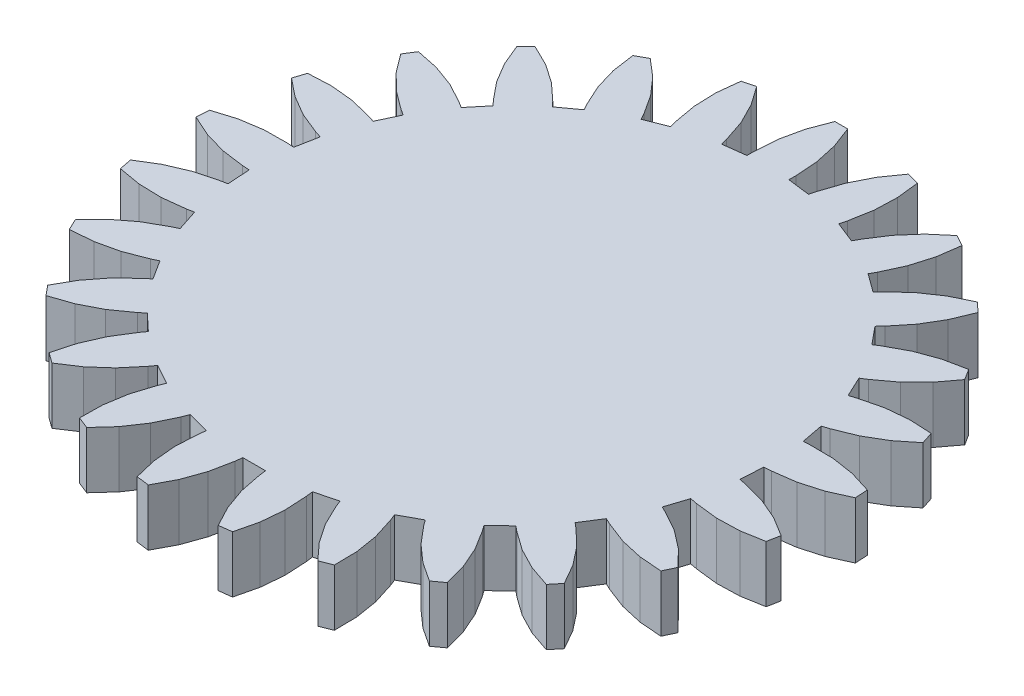
SolidWorks part; units mm, degrees
ref_plane "Alzado" through (0, 0, 0) normal (0, 0, 1) x (1, 0, 0)
ref_plane "Planta" through (0, 0, 0) normal (0, 1, 0) x (1, 0, 0)
ref_plane "Vista lateral" through (0, 0, 0) normal (1, 0, 0) x (0, 0, -1)
ref_plane "Plano1" through (0, 0, 0) normal (0, -1, 0) x (1, 0, 0)
sketch "Croquis1" plane through (0, 0, 0) normal (0, -1, 0) x (1, 0, 0)
  line L0 (59.9729, 13.0996) -> (60.4384, 12.2529)
  line L1 (60.4384, 12.2529) -> (62.1486, 9.6129)
  line L2 (62.1486, 9.6129) -> (64.2209, 7.2465)
  line L3 (64.2209, 7.2465) -> (66.6121, 5.2029)
  line L4 (66.6121, 5.2029) -> (68.1588, 6.0532)
  line L5 (68.1588, 6.0532) -> (67.7145, 9.1672)
  line L6 (67.7145, 9.1672) -> (66.8269, 12.1848)
  line L7 (66.8269, 12.1848) -> (65.5143, 15.0434)
  line L8 (65.5143, 15.0434) -> (65.0488, 15.8901)
  line L9 (65.0488, 15.8901) -> (67.5748, 17.7253)
  line L10 (67.5748, 17.7253) -> (68.2362, 17.021)
  line L11 (68.2362, 17.021) -> (70.5492, 14.8893)
  line L12 (70.5492, 14.8893) -> (73.1449, 13.1126)
  line L13 (73.1449, 13.1126) -> (75.9692, 11.7278)
  line L14 (75.9692, 11.7278) -> (77.2558, 12.936)
  line L15 (77.2558, 12.936) -> (76.0511, 15.8417)
  line L16 (76.0511, 15.8417) -> (74.4409, 18.5438)
  line L17 (74.4409, 18.5438) -> (72.4587, 20.9861)
  line L18 (72.4587, 20.9861) -> (71.7973, 21.6905)
  line L19 (71.7973, 21.6905) -> (73.7875, 24.0962)
  line L20 (73.7875, 24.0962) -> (74.6033, 23.5785)
  line L21 (74.6033, 23.5785) -> (77.3738, 22.089)
  line L22 (77.3738, 22.089) -> (80.3297, 21.0136)
  line L23 (80.3297, 21.0136) -> (83.4097, 20.3748)
  line L24 (83.4097, 20.3748) -> (84.3554, 21.865)
  line L25 (84.3554, 21.865) -> (82.466, 24.3798)
  line L26 (82.466, 24.3798) -> (80.2343, 26.5966)
  line L27 (80.2343, 26.5966) -> (77.707, 28.4692)
  line L28 (77.707, 28.4692) -> (76.8912, 28.9869)
  line L29 (76.8912, 28.9869) -> (78.2206, 31.812)
  line L30 (78.2206, 31.812) -> (79.1395, 31.5135)
  line L31 (79.1395, 31.5135) -> (82.1934, 30.7597)
  line L32 (82.1934, 30.7597) -> (85.3239, 30.4533)
  line L33 (85.3239, 30.4533) -> (88.466, 30.6004)
  line L34 (88.466, 30.6004) -> (89.0114, 32.279)
  line L35 (89.0114, 32.279) -> (86.5559, 34.2449)
  line L36 (86.5559, 34.2449) -> (83.8431, 35.8371)
  line L37 (83.8431, 35.8371) -> (80.9295, 37.0223)
  line L38 (80.9295, 37.0223) -> (80.0106, 37.3209)
  line L39 (80.0106, 37.3209) -> (80.5956, 40.3879)
  line L40 (80.5956, 40.3879) -> (81.5599, 40.3272)
  line L41 (81.5599, 40.3272) -> (84.7053, 40.3567)
  line L42 (84.7053, 40.3567) -> (87.8137, 40.8384)
  line L43 (87.8137, 40.8384) -> (90.8204, 41.7623)
  line L44 (90.8204, 41.7623) -> (90.9313, 43.5238)
  line L45 (90.9313, 43.5238) -> (88.064, 44.8173)
  line L46 (88.064, 44.8173) -> (85.0405, 45.6848)
  line L47 (85.0405, 45.6848) -> (81.9236, 46.1082)
  line L48 (81.9236, 46.1082) -> (80.9593, 46.1688)
  line L49 (80.9593, 46.1688) -> (80.7633, 49.285)
  line L50 (80.7633, 49.285) -> (81.7124, 49.466)
  line L51 (81.7124, 49.466) -> (84.7516, 50.2768)
  line L52 (84.7516, 50.2768) -> (87.6425, 51.5163)
  line L53 (87.6425, 51.5163) -> (90.3251, 53.159)
  line L54 (90.3251, 53.159) -> (89.9943, 54.8927)
  line L55 (89.9943, 54.8927) -> (86.8955, 55.4325)
  line L56 (86.8955, 55.4325) -> (83.7512, 55.5208)
  line L57 (83.7512, 55.5208) -> (80.627, 55.1558)
  line L58 (80.627, 55.1558) -> (79.6779, 54.9747)
  line L59 (79.6779, 54.9747) -> (78.7131, 57.9442)
  line L60 (78.7131, 57.9442) -> (79.5873, 58.3556)
  line L61 (79.5873, 58.3556) -> (82.3294, 59.8967)
  line L62 (82.3294, 59.8967) -> (84.8213, 61.8163)
  line L63 (84.8213, 61.8163) -> (87.011, 64.0744)
  line L64 (87.011, 64.0744) -> (86.2595, 65.6715)
  line L65 (86.2595, 65.6715) -> (83.1238, 65.4236)
  line L66 (83.1238, 65.4236) -> (80.0563, 64.7272)
  line L67 (80.0563, 64.7272) -> (77.121, 63.5967)
  line L68 (77.121, 63.5967) -> (76.2468, 63.1853)
  line L69 (76.2468, 63.1853) -> (74.5738, 65.8216)
  line L70 (74.5738, 65.8216) -> (75.3182, 66.4374)
  line L71 (75.3182, 66.4374) -> (77.5909, 68.6121)
  line L72 (77.5909, 68.6121) -> (79.5271, 71.091)
  line L73 (79.5271, 71.091) -> (81.0865, 73.8228)
  line L74 (81.0865, 73.8228) -> (79.9615, 75.1828)
  line L75 (79.9615, 75.1828) -> (76.9859, 74.1629)
  line L76 (76.9859, 74.1629) -> (74.188, 72.7255)
  line L77 (74.188, 72.7255) -> (71.626, 70.9005)
  line L78 (71.626, 70.9005) -> (70.8816, 70.2847)
  line L79 (70.8816, 70.2847) -> (68.6055, 72.422)
  line L80 (68.6055, 72.422) -> (69.1734, 73.2037)
  line L81 (69.1734, 73.2037) -> (70.8339, 75.8752)
  line L82 (70.8339, 75.8752) -> (72.0928, 78.7578)
  line L83 (72.0928, 78.7578) -> (72.9238, 81.7915)
  line L84 (72.9238, 81.7915) -> (71.4959, 82.829)
  line L85 (71.4959, 82.829) -> (68.8674, 81.1012)
  line L86 (68.8674, 81.1012) -> (66.5149, 79.0131)
  line L87 (66.5149, 79.0131) -> (64.4873, 76.6084)
  line L88 (64.4873, 76.6084) -> (63.9194, 75.8267)
  line L89 (63.9194, 75.8267) -> (61.1833, 77.3309)
  line L90 (61.1833, 77.3309) -> (61.539, 78.2292)
  line L91 (61.539, 78.2292) -> (62.4829, 81.2297)
  line L92 (62.4829, 81.2297) -> (62.9854, 84.3349)
  line L93 (62.9854, 84.3349) -> (63.0358, 87.48)
  line L94 (63.0358, 87.48) -> (61.3948, 88.1297)
  line L95 (61.3948, 88.1297) -> (59.2786, 85.8025)
  line L96 (59.2786, 85.8025) -> (57.5192, 83.195)
  line L97 (57.5192, 83.195) -> (56.1534, 80.3615)
  line L98 (56.1534, 80.3615) -> (55.7977, 79.4632)
  line L99 (55.7977, 79.4632) -> (52.7735, 80.2397)
  line L100 (52.7735, 80.2397) -> (52.8946, 81.1982)
  line L101 (52.8946, 81.1982) -> (53.0627, 84.3393)
  line L102 (53.0627, 84.3393) -> (52.7771, 87.4718)
  line L103 (52.7771, 87.4718) -> (52.0438, 90.5306)
  line L104 (52.0438, 90.5306) -> (50.2927, 90.7518)
  line L105 (50.2927, 90.7518) -> (48.8218, 87.9714)
  line L106 (48.8218, 87.9714) -> (47.7662, 85.0084)
  line L107 (47.7662, 85.0084) -> (47.1479, 81.9242)
  line L108 (47.1479, 81.9242) -> (47.0268, 80.9657)
  line L109 (47.0268, 80.9657) -> (43.9045, 80.9657)
  line L110 (43.9045, 80.9657) -> (43.7834, 81.9242)
  line L111 (43.7834, 81.9242) -> (43.1651, 85.0084)
  line L112 (43.1651, 85.0084) -> (42.1095, 87.9714)
  line L113 (42.1095, 87.9714) -> (40.6385, 90.7518)
  line L114 (40.6385, 90.7518) -> (38.8874, 90.5306)
  line L115 (38.8874, 90.5306) -> (38.1541, 87.4718)
  line L116 (38.1541, 87.4718) -> (37.8686, 84.3393)
  line L117 (37.8686, 84.3393) -> (38.0367, 81.1982)
  line L118 (38.0367, 81.1982) -> (38.1578, 80.2397)
  line L119 (38.1578, 80.2397) -> (35.1336, 79.4632)
  line L120 (35.1336, 79.4632) -> (34.7779, 80.3615)
  line L121 (34.7779, 80.3615) -> (33.412, 83.195)
  line L122 (33.412, 83.195) -> (31.6527, 85.8025)
  line L123 (31.6527, 85.8025) -> (29.5365, 88.1297)
  line L124 (29.5365, 88.1297) -> (27.8954, 87.48)
  line L125 (27.8954, 87.48) -> (27.9459, 84.3349)
  line L126 (27.9459, 84.3349) -> (28.4483, 81.2297)
  line L127 (28.4483, 81.2297) -> (29.3923, 78.2292)
  line L128 (29.3923, 78.2292) -> (29.748, 77.3309)
  line L129 (29.748, 77.3309) -> (27.0119, 75.8267)
  line L130 (27.0119, 75.8267) -> (26.444, 76.6084)
  line L131 (26.444, 76.6084) -> (24.4164, 79.0131)
  line L132 (24.4164, 79.0131) -> (22.0638, 81.1012)
  line L133 (22.0638, 81.1012) -> (19.4354, 82.829)
  line L134 (19.4354, 82.829) -> (18.0074, 81.7915)
  line L135 (18.0074, 81.7915) -> (18.8385, 78.7578)
  line L136 (18.8385, 78.7578) -> (20.0973, 75.8752)
  line L137 (20.0973, 75.8752) -> (21.7578, 73.2037)
  line L138 (21.7578, 73.2037) -> (22.3257, 72.422)
  line L139 (22.3257, 72.422) -> (20.0497, 70.2847)
  line L140 (20.0497, 70.2847) -> (19.3052, 70.9005)
  line L141 (19.3052, 70.9005) -> (16.7433, 72.7255)
  line L142 (16.7433, 72.7255) -> (13.9454, 74.1629)
  line L143 (13.9454, 74.1629) -> (10.9698, 75.1828)
  line L144 (10.9698, 75.1828) -> (9.8447, 73.8228)
  line L145 (9.8447, 73.8228) -> (11.4041, 71.091)
  line L146 (11.4041, 71.091) -> (13.3403, 68.6121)
  line L147 (13.3403, 68.6121) -> (15.613, 66.4374)
  line L148 (15.613, 66.4374) -> (16.3575, 65.8216)
  line L149 (16.3575, 65.8216) -> (14.6845, 63.1853)
  line L150 (14.6845, 63.1853) -> (13.8103, 63.5967)
  line L151 (13.8103, 63.5967) -> (10.8749, 64.7272)
  line L152 (10.8749, 64.7272) -> (7.8075, 65.4236)
  line L153 (7.8075, 65.4236) -> (4.6718, 65.6715)
  line L154 (4.6718, 65.6715) -> (3.9202, 64.0744)
  line L155 (3.9202, 64.0744) -> (6.11, 61.8163)
  line L156 (6.11, 61.8163) -> (8.6019, 59.8967)
  line L157 (8.6019, 59.8967) -> (11.344, 58.3556)
  line L158 (11.344, 58.3556) -> (12.2182, 57.9442)
  line L159 (12.2182, 57.9442) -> (11.2534, 54.9747)
  line L160 (11.2534, 54.9747) -> (10.3043, 55.1558)
  line L161 (10.3043, 55.1558) -> (7.18, 55.5208)
  line L162 (7.18, 55.5208) -> (4.0358, 55.4325)
  line L163 (4.0358, 55.4325) -> (0.9369, 54.8927)
  line L164 (0.9369, 54.8927) -> (0.6062, 53.159)
  line L165 (0.6062, 53.159) -> (3.2887, 51.5163)
  line L166 (3.2887, 51.5163) -> (6.1797, 50.2768)
  line L167 (6.1797, 50.2768) -> (9.2189, 49.466)
  line L168 (9.2189, 49.466) -> (10.168, 49.285)
  line L169 (10.168, 49.285) -> (9.9719, 46.1688)
  line L170 (9.9719, 46.1688) -> (9.0077, 46.1082)
  line L171 (9.0077, 46.1082) -> (5.8908, 45.6848)
  line L172 (5.8908, 45.6848) -> (2.8673, 44.8173)
  line L173 (2.8673, 44.8173) -> (0, 43.5238)
  line L174 (0, 43.5238) -> (0.1108, 41.7623)
  line L175 (0.1108, 41.7623) -> (3.1176, 40.8384)
  line L176 (3.1176, 40.8384) -> (6.226, 40.3567)
  line L177 (6.226, 40.3567) -> (9.3714, 40.3272)
  line L178 (9.3714, 40.3272) -> (10.3356, 40.3879)
  line L179 (10.3356, 40.3879) -> (10.9207, 37.3209)
  line L180 (10.9207, 37.3209) -> (10.0018, 37.0223)
  line L181 (10.0018, 37.0223) -> (7.0881, 35.8371)
  line L182 (7.0881, 35.8371) -> (4.3753, 34.2449)
  line L183 (4.3753, 34.2449) -> (1.9199, 32.279)
  line L184 (1.9199, 32.279) -> (2.4653, 30.6004)
  line L185 (2.4653, 30.6004) -> (5.6073, 30.4533)
  line L186 (5.6073, 30.4533) -> (8.7379, 30.7597)
  line L187 (8.7379, 30.7597) -> (11.7917, 31.5135)
  line L188 (11.7917, 31.5135) -> (12.7106, 31.812)
  line L189 (12.7106, 31.812) -> (14.04, 28.9869)
  line L190 (14.04, 28.9869) -> (13.2243, 28.4692)
  line L191 (13.2243, 28.4692) -> (10.6969, 26.5966)
  line L192 (10.6969, 26.5966) -> (8.4653, 24.3798)
  line L193 (8.4653, 24.3798) -> (6.5758, 21.865)
  line L194 (6.5758, 21.865) -> (7.5216, 20.3748)
  line L195 (7.5216, 20.3748) -> (10.6015, 21.0136)
  line L196 (10.6015, 21.0136) -> (13.5575, 22.089)
  line L197 (13.5575, 22.089) -> (16.328, 23.5785)
  line L198 (16.328, 23.5785) -> (17.1438, 24.0962)
  line L199 (17.1438, 24.0962) -> (19.134, 21.6905)
  line L200 (19.134, 21.6905) -> (18.4726, 20.9861)
  line L201 (18.4726, 20.9861) -> (16.4903, 18.5438)
  line L202 (16.4903, 18.5438) -> (14.8801, 15.8417)
  line L203 (14.8801, 15.8417) -> (13.6754, 12.936)
  line L204 (13.6754, 12.936) -> (14.9621, 11.7278)
  line L205 (14.9621, 11.7278) -> (17.7864, 13.1126)
  line L206 (17.7864, 13.1126) -> (20.382, 14.8893)
  line L207 (20.382, 14.8893) -> (22.695, 17.021)
  line L208 (22.695, 17.021) -> (23.3564, 17.7253)
  line L209 (23.3564, 17.7253) -> (25.8824, 15.8901)
  line L210 (25.8824, 15.8901) -> (25.417, 15.0434)
  line L211 (25.417, 15.0434) -> (24.1044, 12.1848)
  line L212 (24.1044, 12.1848) -> (23.2167, 9.1672)
  line L213 (23.2167, 9.1672) -> (22.7725, 6.0532)
  line L214 (22.7725, 6.0532) -> (24.3192, 5.2029)
  line L215 (24.3192, 5.2029) -> (26.7104, 7.2465)
  line L216 (26.7104, 7.2465) -> (28.7826, 9.6129)
  line L217 (28.7826, 9.6129) -> (30.4929, 12.2529)
  line L218 (30.4929, 12.2529) -> (30.9583, 13.0996)
  line L219 (30.9583, 13.0996) -> (33.8614, 11.9502)
  line L220 (33.8614, 11.9502) -> (33.6211, 11.0143)
  line L221 (33.6211, 11.0143) -> (33.0606, 7.9192)
  line L222 (33.0606, 7.9192) -> (32.9513, 4.7756)
  line L223 (32.9513, 4.7756) -> (33.2955, 1.6489)
  line L224 (33.2955, 1.6489) -> (35.005, 1.21)
  line L225 (35.005, 1.21) -> (36.8129, 3.7841)
  line L226 (36.8129, 3.7841) -> (38.2315, 6.5915)
  line L227 (38.2315, 6.5915) -> (39.2315, 9.5738)
  line L228 (39.2315, 9.5738) -> (39.4718, 10.5097)
  line L229 (39.4718, 10.5097) -> (42.5694, 10.1183)
  line L230 (42.5694, 10.1183) -> (42.5694, 9.1522)
  line L231 (42.5694, 9.1522) -> (42.7963, 6.0148)
  line L232 (42.7963, 6.0148) -> (43.4722, 2.9428)
  line L233 (43.4722, 2.9428) -> (44.5831, 0)
  line L234 (44.5831, 0) -> (46.3481, 0)
  line L235 (46.3481, 0) -> (47.459, 2.9428)
  line L236 (47.459, 2.9428) -> (48.1349, 6.0148)
  line L237 (48.1349, 6.0148) -> (48.3618, 9.1522)
  line L238 (48.3618, 9.1522) -> (48.3618, 10.1183)
  line L239 (48.3618, 10.1183) -> (51.4595, 10.5097)
  line L240 (51.4595, 10.5097) -> (51.6998, 9.5738)
  line L241 (51.6998, 9.5738) -> (52.6997, 6.5915)
  line L242 (52.6997, 6.5915) -> (54.1184, 3.7841)
  line L243 (54.1184, 3.7841) -> (55.9262, 1.21)
  line L244 (55.9262, 1.21) -> (57.6358, 1.6489)
  line L245 (57.6358, 1.6489) -> (57.9799, 4.7756)
  line L246 (57.9799, 4.7756) -> (57.8706, 7.9192)
  line L247 (57.8706, 7.9192) -> (57.3102, 11.0143)
  line L248 (57.3102, 11.0143) -> (57.0699, 11.9502)
  line L249 (57.0699, 11.9502) -> (59.9729, 13.0996)
extrude "Saliente-Extruir1" add sketch "Croquis1" against normal blind 7.8
sketch "Croquis2" plane through (0, 0, 0) normal (0, -1, 0) x (1, 0, 0)
  line L0 (63.669, 47.6756) -> (63.2406, 47.9759)
  line L1 (63.2406, 47.9759) -> (50.2386, 50.1489)
  line L2 (50.2386, 50.1489) -> (48.0656, 63.1509)
  line L3 (48.0656, 63.1509) -> (47.7653, 63.5793)
  line L4 (47.7653, 63.5793) -> (47.3952, 63.9491)
  line L5 (47.3952, 63.9491) -> (46.9665, 64.249)
  line L6 (46.9665, 64.249) -> (46.4922, 64.47)
  line L7 (46.4922, 64.47) -> (45.9868, 64.6053)
  line L8 (45.9868, 64.6053) -> (45.4656, 64.6509)
  line L9 (45.4656, 64.6509) -> (44.9444, 64.6053)
  line L10 (44.9444, 64.6053) -> (44.439, 64.47)
  line L11 (44.439, 64.47) -> (43.9648, 64.249)
  line L12 (43.9648, 64.249) -> (43.5361, 63.9491)
  line L13 (43.5361, 63.9491) -> (43.166, 63.5793)
  line L14 (43.166, 63.5793) -> (42.8656, 63.1509)
  line L15 (42.8656, 63.1509) -> (40.6927, 50.1489)
  line L16 (40.6927, 50.1489) -> (27.6906, 47.9759)
  line L17 (27.6906, 47.9759) -> (27.2622, 47.6756)
  line L18 (27.2622, 47.6756) -> (26.8925, 47.3054)
  line L19 (26.8925, 47.3054) -> (26.5925, 46.8767)
  line L20 (26.5925, 46.8767) -> (26.3715, 46.4025)
  line L21 (26.3715, 46.4025) -> (26.2362, 45.8971)
  line L22 (26.2362, 45.8971) -> (26.1906, 45.3759)
  line L23 (26.1906, 45.3759) -> (26.2362, 44.8547)
  line L24 (26.2362, 44.8547) -> (26.3715, 44.3493)
  line L25 (26.3715, 44.3493) -> (26.5925, 43.8751)
  line L26 (26.5925, 43.8751) -> (26.8925, 43.4464)
  line L27 (26.8925, 43.4464) -> (27.2622, 43.0763)
  line L28 (27.2622, 43.0763) -> (27.6906, 42.7759)
  line L29 (27.6906, 42.7759) -> (40.6927, 40.6029)
  line L30 (40.6927, 40.6029) -> (42.8656, 27.6009)
  line L31 (42.8656, 27.6009) -> (43.166, 27.1725)
  line L32 (43.166, 27.1725) -> (43.5361, 26.8027)
  line L33 (43.5361, 26.8027) -> (43.9648, 26.5028)
  line L34 (43.9648, 26.5028) -> (44.439, 26.2818)
  line L35 (44.439, 26.2818) -> (44.9444, 26.1465)
  line L36 (44.9444, 26.1465) -> (45.4656, 26.1009)
  line L37 (45.4656, 26.1009) -> (45.9868, 26.1465)
  line L38 (45.9868, 26.1465) -> (46.4922, 26.2818)
  line L39 (46.4922, 26.2818) -> (46.9665, 26.5028)
  line L40 (46.9665, 26.5028) -> (47.3952, 26.8027)
  line L41 (47.3952, 26.8027) -> (47.7653, 27.1725)
  line L42 (47.7653, 27.1725) -> (48.0656, 27.6009)
  line L43 (48.0656, 27.6009) -> (50.2386, 40.6029)
  line L44 (50.2386, 40.6029) -> (63.2406, 42.7759)
  line L45 (63.2406, 42.7759) -> (63.669, 43.0763)
  line L46 (63.669, 43.0763) -> (64.0388, 43.4464)
  line L47 (64.0388, 43.4464) -> (64.3387, 43.8751)
  line L48 (64.3387, 43.8751) -> (64.5597, 44.3493)
  line L49 (64.5597, 44.3493) -> (64.6951, 44.8547)
  line L50 (64.6951, 44.8547) -> (64.7406, 45.3759)
  line L51 (64.7406, 45.3759) -> (64.6951, 45.8971)
  line L52 (64.6951, 45.8971) -> (64.5597, 46.4025)
  line L53 (64.5597, 46.4025) -> (64.3387, 46.8767)
  line L54 (64.3387, 46.8767) -> (64.0388, 47.3054)
  line L55 (64.0388, 47.3054) -> (63.669, 47.6756)
extrude "Cortar-Extruir1" cut sketch "Croquis2" against normal blind 7.4
